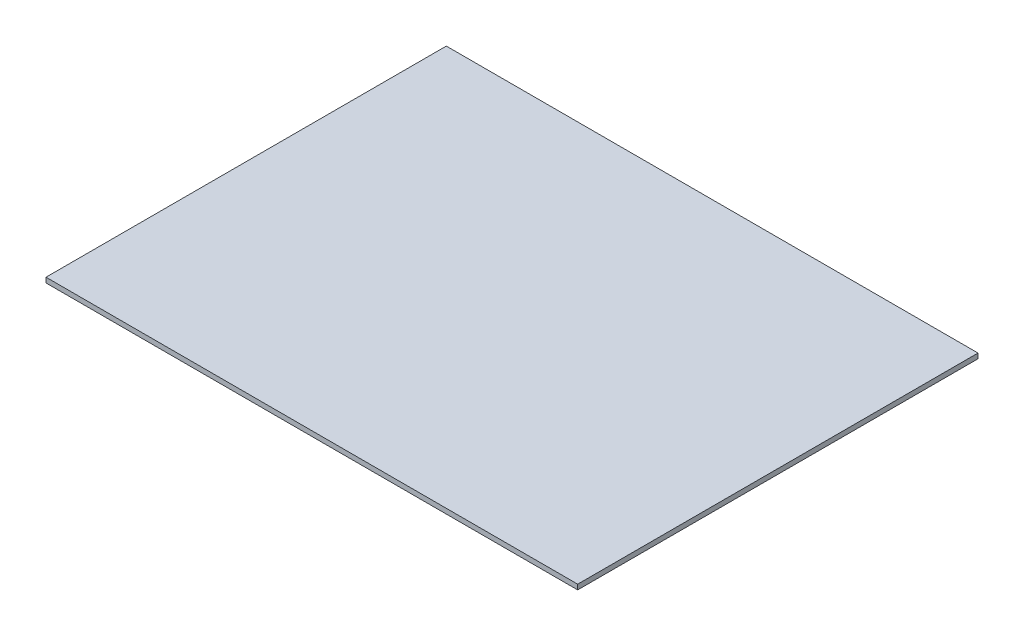
SolidWorks part; units mm, degrees
ref_plane "Спереди" through (0, 0, 0) normal (0, 0, 1) x (1, 0, 0)
ref_plane "Сверху" through (0, 0, 0) normal (0, 1, 0) x (1, 0, 0)
ref_plane "Справа" through (0, 0, 0) normal (1, 0, 0) x (0, 0, -1)
sketch "Эскиз1" plane through (0, 0, 0) normal (0, 1, 0) x (1, 0, 0)
  line L1 (-212.5, -160) -> (212.5, -160)
  line L2 (-212.5, -160) -> (-212.5, 160)
  line L3 (-212.5, 160) -> (212.5, 160)
  line L4 (212.5, -160) -> (212.5, 160)
  line L5 (-212.5, -160) -> (212.5, 160) construction
  line L6 (-212.5, 160) -> (212.5, -160) construction
  point P0 (0, 0)
  dimension "D1" = 320
  dimension "D2" = 425
extrude "Бобышка-Вытянуть1" add sketch "Эскиз1" along normal blind 4
